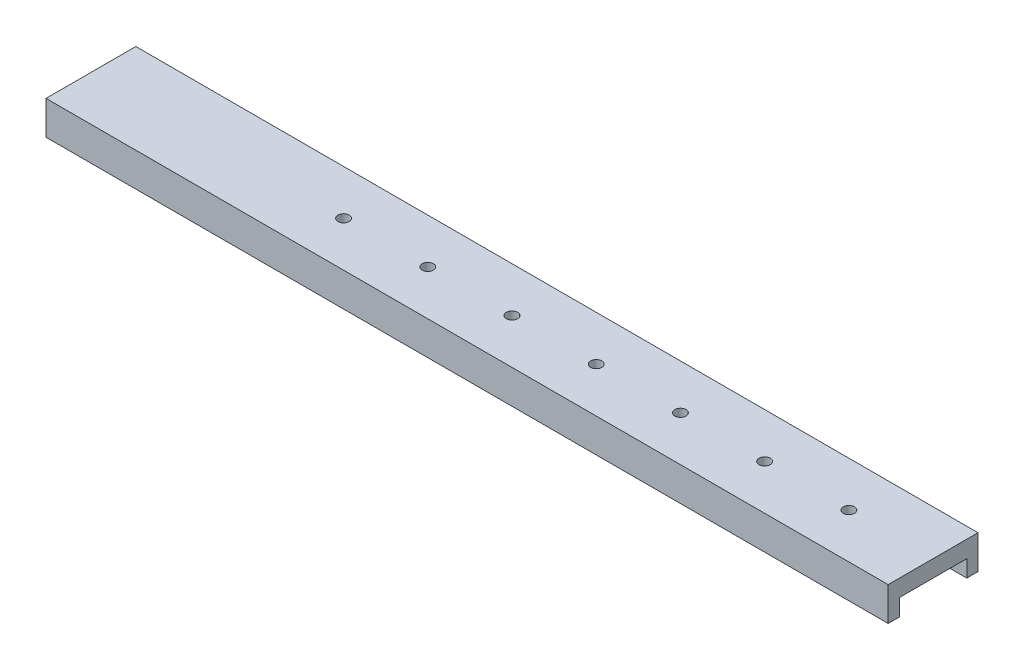
SolidWorks part; units mm, degrees
ref_plane "Ön Düzlem" through (0, 0, 0) normal (0, 0, 1) x (1, 0, 0)
ref_plane "Üst Düzlem" through (0, 0, 0) normal (0, 1, 0) x (1, 0, 0)
ref_plane "Sağ Düzlem" through (0, 0, 0) normal (1, 0, 0) x (0, 0, -1)
sketch "Çizim2" plane through (0, 0, 0) normal (0, 1, 0) x (1, 0, 0)
  line L1 (-375, -40) -> (375, -40)
  line L2 (-375, -40) -> (-375, 40)
  line L3 (-375, 40) -> (375, 40)
  line L4 (375, -40) -> (375, 40)
  line L5 (-375, -40) -> (375, 40) construction
  line L6 (-375, 40) -> (375, -40) construction
  circle A0 centre (300, 0) radius 5
  circle A1 centre (225, 0) radius 5
  circle A2 centre (150, 0) radius 5
  circle A3 centre (75, 0) radius 5
  circle A4 centre (0, 0) radius 5
  circle A5 centre (-75, 0) radius 5
  circle A6 centre (-150, 0) radius 5
  point P0 (0, 0)
  dimension "D3" = 10
  dimension "D5" = 75
  dimension "D6" = 40
  dimension "D1" = 80
  dimension "D2" = 750
  dimension "D4" = 5
  dimension "D7" = 3
extrude "Yükseklik-Ekstrüzyon1" add sketch "Çizim2" against normal blind 30
sketch "Çizim3" plane through (375, 0, 0) normal (1, 0, 0) x (0, 0, -1)
  line L0 (-30, -15) -> (-30, -30)
  line L1 (-40, -30) -> (40, -30) construction
  line L2 (-30, -30) -> (30, -30)
  line L3 (30, -30) -> (30, -15)
  line L4 (30, -15) -> (-30, -15)
  line L5 (-40, -30) -> (-40, 0) construction
  line L6 (40, -30) -> (40, 0) construction
  dimension "D1" = 10
  dimension "D2" = 10
  dimension "D3" = 15
extrude "Kes-Ekstrüzyon1" cut sketch "Çizim3" against normal blind 600
